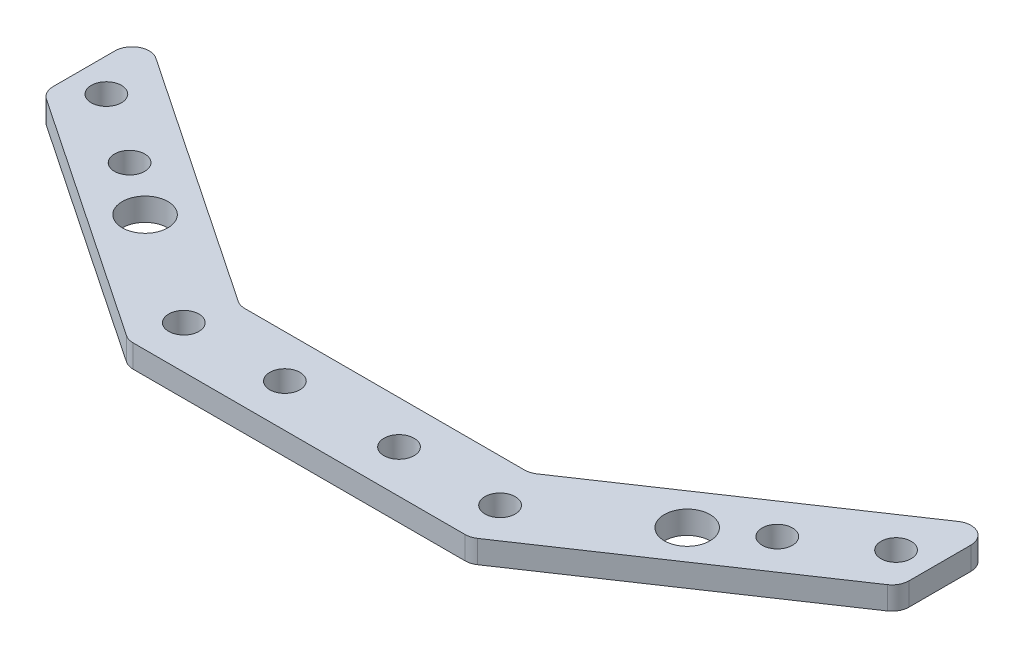
SolidWorks part; units mm, degrees
material "Hexcel AS4C (3000 丝)"
ref_plane "前视基准面" through (0, 0, 0) normal (0, 0, 1) x (1, 0, 0)
ref_plane "上视基准面" through (0, 0, 0) normal (0, 1, 0) x (1, 0, 0)
ref_plane "右视基准面" through (0, 0, 0) normal (1, 0, 0) x (0, 0, -1)
sketch "草图1" plane through (0, 0, 0) normal (0, 1, 0) x (1, 0, 0)
  line L0 (0, 0) -> (275, 0) construction
  line L1 (0, 0) -> (0, 275) construction
  line L2 (0, 0) -> (194.4544, 194.4544) construction
  circle A0 centre (0, 0) radius 255
  circle A1 centre (0, 0) radius 275
  dimension "D1" = 510
  dimension "D2" = 20
  dimension "D3" = 45
extrude "凸台-拉伸1" add sketch "草图1" along normal blind 10
sketch "草图2" plane through (0, 10, 0) normal (0, 1, 0) x (1, 0, 0)
  line L0 (0, 0) -> (275, 0) construction
  line L1 (164.7559, 164.7559) -> (217.7889, 111.7229) construction
  line L2 (164.7559, 164.7559) -> (111.7229, 217.7889) construction
  line L3 (0, 0) -> (164.7559, 164.7559) construction
  line L4 (111.7229, 217.7889) -> (121.6224, 227.6884) construction
  line L5 (217.7889, 111.7229) -> (227.6884, 121.6224) construction
  line L6 (0, 0) -> (240.1716, 111.9938) construction
  line L7 (0, 0) -> (111.9938, 240.1716) construction
  line L8 (0, 0) -> (0, 275) construction
  line L9 (0, 185) -> (30, 185)
  line L10 (-110.5251, 257.2629) -> (-25.4233, 200)
  line L11 (111.9938, 240.1716) -> (30, 185)
  line L12 (0, 200) -> (-25.4233, 200)
  line L13 (240.1716, 111.9938) -> (185, 30)
  line L14 (185, 0) -> (185, 30)
  line L15 (-111.9938, 240.1716) -> (-30, 185)
  line L16 (0, 200) -> (25.4233, 200)
  line L17 (110.5251, 257.2629) -> (25.4233, 200)
  line L18 (257.2629, 110.5251) -> (200, 25.4233)
  line L19 (200, 0) -> (200, 25.4233)
  line L20 (0, 185) -> (-30, 185)
  line L21 (0, 185) -> (-30, 185) construction
  line L22 (0, 200) -> (-30, 200) construction
  line L23 (200, 0) -> (200, -1.5596) construction
  line L24 (185, 0) -> (185, -1.5596) construction
  line L25 (-200, -25.4233) -> (-200, 25.4233)
  line L26 (-257.2629, 110.5251) -> (-200, 25.4233)
  line L27 (-185, -30) -> (-185, 30)
  line L28 (-240.1716, 111.9938) -> (-185, 30)
  line L29 (185, 0) -> (185, -30)
  line L30 (200, 0) -> (200, -25.4233)
  line L31 (257.2629, -110.5251) -> (200, -25.4233)
  line L32 (240.1716, -111.9938) -> (185, -30)
  line L33 (164.7559, -164.7559) -> (111.7229, -217.7889) construction
  line L34 (110.5251, -257.2629) -> (25.4233, -200)
  line L35 (111.9938, -240.1716) -> (30, -185)
  line L36 (0, -185) -> (-30, -185)
  line L37 (0, -200) -> (-25.4233, -200)
  line L38 (0, -200) -> (25.4233, -200)
  line L39 (0, -185) -> (30, -185)
  line L40 (-111.9938, -240.1716) -> (-30, -185)
  line L41 (-110.5251, -257.2629) -> (-25.4233, -200)
  line L42 (-240.1716, -111.9938) -> (-185, -30)
  line L43 (-257.2629, -110.5251) -> (-200, -25.4233)
  circle A0 centre (0, 0) radius 275 construction
  arc A2 (111.9938, 240.1716) -> (240.1716, 111.9938) centre (0, 0) cw
  arc A3 (110.5251, 257.2629) -> (257.2629, 110.5251) centre (0, 0) cw
  arc A4 (-110.5251, 257.2629) -> (-257.2629, 110.5251) centre (0, 0) ccw
  arc A5 (-111.9938, 240.1716) -> (-240.1716, 111.9938) centre (0, 0) ccw
  arc A6 (110.5251, -257.2629) -> (257.2629, -110.5251) centre (0, 0) ccw
  arc A7 (111.9938, -240.1716) -> (240.1716, -111.9938) centre (0, 0) ccw
  arc A8 (-111.9938, -240.1716) -> (-240.1716, -111.9938) centre (0, 0) cw
  arc A9 (-110.5251, -257.2629) -> (-257.2629, -110.5251) centre (0, 0) cw
  point P60 (-185, 0)
  point P61 (-200, 0)
  dimension "D5" = 14
  dimension "D7" = 265
  dimension "D1" = 233
  dimension "D3" = 75
  dimension "D4" = 75
  dimension "D6" = 14
  dimension "D8" = 15
  dimension "D9" = 20
  dimension "D10" = 30
  dimension "D11" = 185
extrude "凸台-拉伸2" add sketch "草图2" along normal blind 10 separate body
sketch "草图8" plane through (0, 20, 0) normal (0, 1, 0) x (1, 0, 0)
  line L0 (0, 0) -> (-187.3833, 187.3833) construction
  line L1 (-243.7881, 137.7221) -> (-232.755, 126.689) construction
  line L2 (-137.7221, 243.7881) -> (-126.689, 232.755) construction
  line L3 (0, 0) -> (0, 200) construction
  line L4 (25.4233, 200) -> (-25.4233, 200) construction
  line L5 (-75, 233.3589) -> (-75, 215.2794) construction
  line L6 (75, 233.3589) -> (75, 215.2794) construction
  line L7 (-30, 185) -> (-111.9938, 240.1716) construction
  line L8 (-25.4233, 200) -> (-110.5251, 257.2629) construction
  line L9 (0, 0) -> (214.4019, 0) construction
  line L10 (200, -25.4233) -> (200, 25.4233) construction
  line L11 (-27.7116, 192.5) -> (-110.5251, 248.2231) construction
  line L12 (-10, 192.5) -> (-27.7116, 192.5) construction
  line L13 (-110.5251, 257.2629) -> (-110.5251, 248.2231) construction
  line L14 (-257.2629, 110.5251) -> (-248.2231, 110.5251) construction
  line L15 (-192.5, 27.7116) -> (-248.2231, 110.5251) construction
  line L16 (-233.3589, 75) -> (-215.2794, 75) construction
  line L17 (233.3589, 75) -> (215.2794, 75) construction
  line L18 (192.5, 27.7116) -> (248.2231, 110.5251) construction
  line L19 (257.2629, 110.5251) -> (248.2231, 110.5251) construction
  line L20 (243.7881, 137.7221) -> (232.755, 126.689) construction
  line L21 (137.7221, 243.7881) -> (126.689, 232.755) construction
  line L22 (0, 0) -> (187.3833, 187.3833) construction
  line L23 (110.5251, 257.2629) -> (110.5251, 248.2231) construction
  line L24 (27.7116, 192.5) -> (110.5251, 248.2231) construction
  line L25 (75, 233.3589) -> (75, 215.2794) construction
  arc A0 (-111.9938, 240.1716) -> (-240.1716, 111.9938) centre (0, 0) ccw construction
  arc A1 (-110.5251, 257.2629) -> (-257.2629, 110.5251) centre (0, 0) ccw construction
  circle A2 centre (-10, 192.5) radius 2.65
  circle A3 centre (10, 192.5) radius 2.65
  circle A4 centre (-10, -192.5) radius 2.65
  circle A5 centre (10, -192.5) radius 2.65
  circle A6 centre (192.5, 10) radius 2.65
  circle A8 centre (192.5, -10) radius 2.65
  circle A9 centre (-192.5, 10) radius 2.65
  circle A10 centre (-192.5, -10) radius 2.65
  circle A11 centre (-110.5251, 248.2231) radius 1.65
  circle A12 centre (-27.7116, 192.5) radius 2.65
  circle A13 centre (-44.3049, 203.6652) radius 2.65 construction
  circle A14 centre (-56.7499, 212.0391) radius 2.65
  circle A15 centre (-69.1949, 220.413) radius 2.65
  circle A16 centre (-81.6399, 228.787) radius 2.65
  arc A17 (-238.2716, 132.2055) -> (-128.8116, 240.1233) centre (0, 0) cw construction
  circle A18 centre (-146.077, 230.0286) radius 2.15
  circle A19 centre (-164.4155, 217.2997) radius 2.15
  circle A20 centre (-183.6389, 201.3166) radius 2.15
  circle A21 centre (-201.3166, 183.6389) radius 2.15
  circle A22 centre (-217.2997, 164.4155) radius 2.15
  circle A23 centre (-230.0286, 146.077) radius 2.15
  circle A24 centre (-128.8116, 240.1233) radius 2.65
  circle A25 centre (-240.1233, 128.8116) radius 2.65
  circle A26 centre (-228.787, 81.6399) radius 2.65
  circle A27 centre (-220.413, 69.1949) radius 2.65
  circle A28 centre (-212.0391, 56.7499) radius 2.65
  circle A29 centre (-203.6652, 44.3049) radius 2.65
  circle A30 centre (-192.5, 27.7116) radius 2.65
  circle A31 centre (-248.2231, 110.5251) radius 1.65
  circle A32 centre (192.5, 27.7116) radius 2.65
  circle A33 centre (248.2231, 110.5251) radius 1.65
  circle A34 centre (203.6652, 44.3049) radius 2.65
  circle A35 centre (212.0391, 56.7499) radius 2.65
  circle A36 centre (220.413, 69.1949) radius 2.65
  circle A37 centre (228.787, 81.6399) radius 2.65
  circle A38 centre (240.1233, 128.8116) radius 2.65
  circle A39 centre (230.0286, 146.077) radius 2.15
  arc A40 (238.2716, 132.2055) -> (128.8116, 240.1233) centre (0, 0) ccw construction
  circle A41 centre (128.8116, 240.1233) radius 2.65
  circle A42 centre (201.3166, 183.6389) radius 2.15
  circle A43 centre (183.6389, 201.3166) radius 2.15
  circle A44 centre (164.4155, 217.2997) radius 2.15
  circle A45 centre (146.077, 230.0286) radius 2.15
  circle A46 centre (81.6399, 228.787) radius 2.65
  circle A47 centre (69.1949, 220.413) radius 2.65
  circle A48 centre (56.7499, 212.0391) radius 2.65
  circle A49 centre (44.3049, 203.6652) radius 2.65 construction
  circle A50 centre (110.5251, 248.2231) radius 1.65
  circle A51 centre (27.7116, 192.5) radius 2.65
  circle A52 centre (217.2997, 164.4155) radius 2.15
  dimension "D1" = 75
  dimension "D3" = 5.3
  dimension "D4" = 20
  dimension "D5" = 7.5
  dimension "D6" = 5.3
  dimension "D7" = 20
  dimension "D8" = 7.5
  dimension "D10" = 3.3
  dimension "D11" = 5.3
  dimension "D12" = 15
  dimension "D13" = 15
  dimension "D14" = 15
  dimension "D15" = 20
  dimension "D16" = 4.3
  dimension "D17" = 20
  dimension "D18" = 25
  dimension "D19" = 20
  dimension "D20" = 25
  dimension "D21" = 25
  dimension "D22" = 5.3
  dimension "D23" = 20
  dimension "D2" = 75
  dimension "D9" = 7.5
extrude "切除-拉伸1" cut sketch "草图8" against normal through all
sketch "草图9" plane through (0, 20, 0) normal (0, 1, 0) x (1, 0, 0)
  line L0 (-75, 233.3589) -> (-75, 215.2794)
  line L1 (-75, 215.2794) -> (-30, 185)
  line L2 (-30, 185) -> (30, 185)
  line L3 (30, 185) -> (-30, 185) construction
  line L4 (-75, 233.3589) -> (-25.4233, 200)
  line L5 (-25.4233, 200) -> (25.4233, 200)
  line L6 (0, 0) -> (0, 286.5456) construction
  line L7 (75, 233.3589) -> (25.4233, 200)
  line L8 (75, 215.2794) -> (30, 185)
  line L9 (75, 233.3589) -> (75, 215.2794)
  point P17 (0, 200)
  point P19 (0, 185)
extrude "切除-拉伸2" cut sketch "草图9" against normal through all flip side to cut
sketch "草图10" plane through (0, 0, -185) normal (0, 0, 1) x (1, 0, 0)
  line L1 (-75, -16) -> (75, -16)
  line L2 (-75, -16) -> (-75, 16)
  line L3 (-75, 16) -> (75, 16)
  line L4 (75, -16) -> (75, 16)
  line L5 (-75, -16) -> (75, 16) construction
  line L6 (-75, 16) -> (75, -16) construction
  line L8 (75, 20) -> (30, 20) construction
  line L9 (75, 10) -> (75, 20) construction
  point P0 (0, 0)
  dimension "D1" = 4
extrude "切除-拉伸3" cut sketch "草图10" against normal through all
sketch "草图11" plane through (0, 10, 0) normal (0, 1, 0) x (1, 0, 0)
  circle A0 centre (0, 0) radius 255
  circle A1 centre (0, 0) radius 275
extrude "切除-拉伸4" cut sketch "草图11" against normal through all both and the other way through all
fillet "圆角1" radius 3 8 edges at (-25.4233, 18, -200) (25.4233, 18, -200) (75, 18, -233.3589) (75, 18, -215.2794) (30, 18, -185) (-30, 18, -185) (-75, 18, -215.2794) (-75, 18, -233.3589)
sketch "草图12" plane through (0, 16, 0) normal (0, -1, 0) x (1, 0, 0)
  line L0 (0, -200) -> (0, -177.5419) construction
  line L1 (24.5079, -200) -> (-24.5079, -200) construction
  line L2 (75, -227.7244) -> (75, -216.8766) construction
  line L3 (29.0847, -185) -> (-29.0847, -185) construction
  circle A0 centre (-47.1741, -205.9832) radius 4.5
  circle A1 centre (47.1741, -205.9832) radius 4.5
  dimension "D1" = 47.1741
  dimension "D2" = 5.9832
  dimension "D3" = 9
extrude "切除-拉伸5" [suppressed] cut sketch "草图12" against normal through all
sketch "草图13" plane through (0, 16, 0) normal (0, -1, 0) x (1, 0, 0)
  line L0 (0, -200) -> (0, -159.6906) construction
  line L1 (24.5079, -200) -> (-24.5079, -200) construction
  circle A0 centre (-47.5, -205.5) radius 4
  circle A1 centre (47.5, -205.5) radius 4
  dimension "D2" = 47.5
  dimension "D3" = 8
  dimension "D1" = 5.5
extrude "切除-拉伸6" cut sketch "草图13" against normal through all
